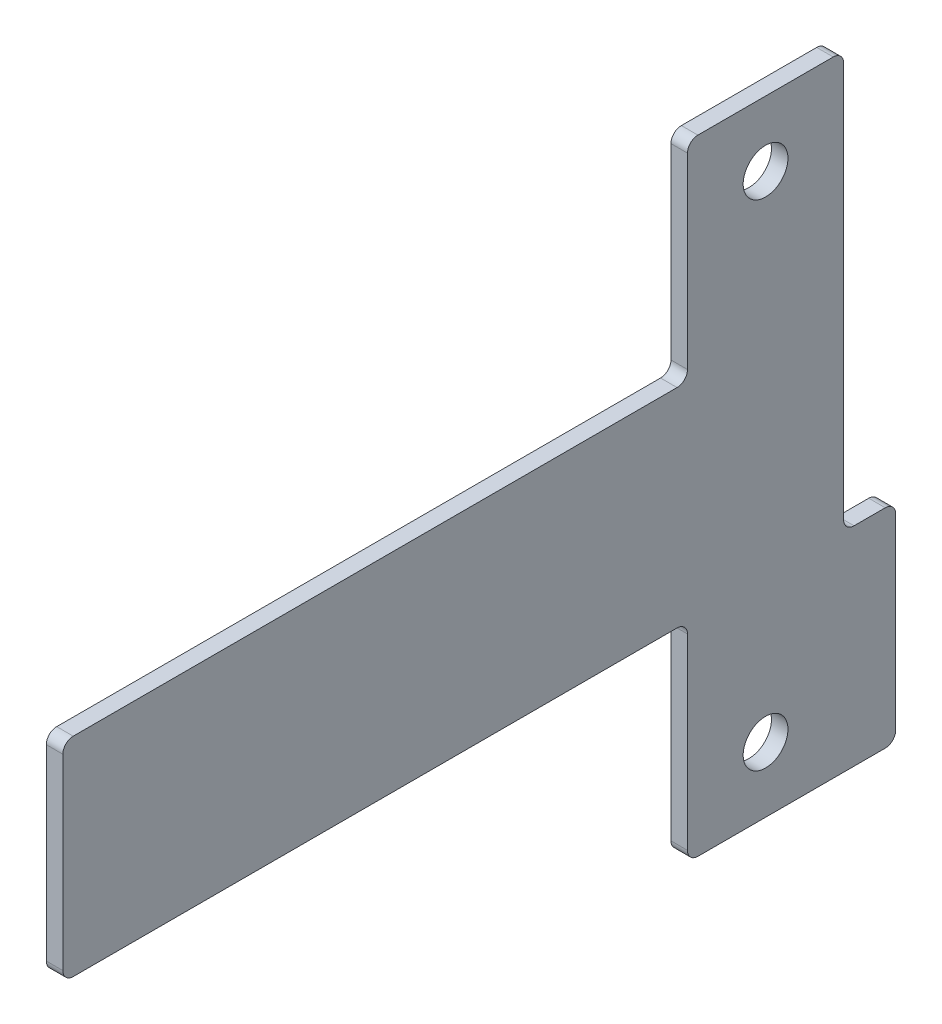
SolidWorks part; units mm, degrees
material "E-Glass Fiber"
ref_plane "Front Plane" through (0, 0, 0) normal (0, 0, 1) x (1, 0, 0)
ref_plane "Top Plane" through (0, 0, 0) normal (0, 1, 0) x (1, 0, 0)
ref_plane "Right Plane" through (0, 0, 0) normal (1, 0, 0) x (0, 0, -1)
sketch "Sketch1" plane through (0, 0, 0) normal (1, 0, 0) x (0, 0, -1)
  line L5 (-7.5, 30) -> (7.5, 30)
  line L6 (7.5, 30) -> (7.5, -30) construction
  line L20 (7.5, -30) -> (-7.5, -30)
  line L21 (-7.5, -30) -> (-7.5, -10)
  line L22 (-7.5, -10) -> (-67.5, -10)
  line L25 (-67.5, -10) -> (-67.5, 10)
  line L26 (-67.5, 10) -> (-7.5, 10)
  line L27 (-7.5, 10) -> (-7.5, 30)
  line L28 (0, 23.75) -> (0, -23.75) construction
  line L29 (-67.5, 0) -> (7.5, 0) construction
  line L30 (-7.5, 10) -> (-7.5, -10) construction
  line L31 (7.5, 30) -> (7.5, -10)
  line L32 (7.5, -10) -> (12.5, -10)
  line L33 (12.5, -10) -> (12.5, -30)
  line L34 (12.5, -30) -> (7.5, -30)
  circle A0 centre (0, 23.75) radius 2.15
  circle A1 centre (0, -23.75) radius 2.15
  point P6 (0, 30)
  point P15 (7.5, 0)
  point P16 (-7.5, 0)
  point P17 (0, 0)
  point P20 (0, 0)
  dimension "D1" = 4.3
  dimension "D2" = 47.5
  dimension "D3" = 60
  dimension "D4" = 20
  dimension "D5" = 75
  dimension "D6" = 15
  dimension "D7" = 5
extrude "Boss-Extrude1" add sketch "Sketch1" along normal blind 1.5875
fillet "Fillet1" radius 1 10 edges at (0.7937, 10, 67.5) (0.7937, -10, 7.5) (0.7937, -30, 7.5) (0.7937, 30, 7.5) (0.7937, 10, 7.5) (0.7937, -10, 67.5) (0.7937, -30, -12.5) (0.7937, -10, -12.5) (0.7937, -10, -7.5) (0.7937, 30, -7.5)
